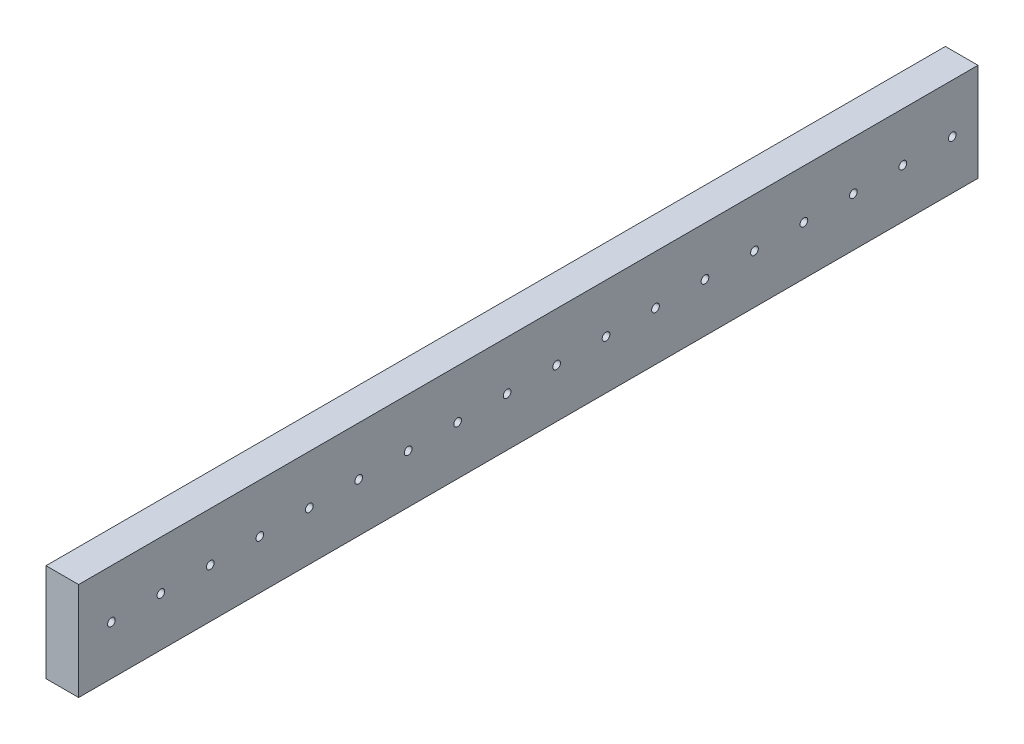
SolidWorks part; units mm, degrees
ref_plane "Alzado" through (0, 0, 0) normal (0, 0, 1) x (1, 0, 0)
ref_plane "Planta" through (0, 0, 0) normal (0, 1, 0) x (1, 0, 0)
ref_plane "Vista lateral" through (0, 0, 0) normal (1, 0, 0) x (0, 0, -1)
sketch "Croquis2" plane through (0, 0, 0) normal (0, 0, 1) x (1, 0, 0)
  line L1 (-12.7, -38.1) -> (12.7, -38.1)
  line L2 (-12.7, -38.1) -> (-12.7, 38.1)
  line L3 (-12.7, 38.1) -> (12.7, 38.1)
  line L4 (12.7, -38.1) -> (12.7, 38.1)
  line L5 (-12.7, -38.1) -> (12.7, 38.1) construction
  line L6 (-12.7, 38.1) -> (12.7, -38.1) construction
  point P0 (0, 0)
  dimension "D1" = 25.4
  dimension "D2" = 76.2
extrude "Saliente-Extruir1" add sketch "Croquis2" against normal blind 700
sketch "Croquis3" plane through (-12.7, 0, 0) normal (-1, 0, 0) x (0, 0, 1)
  line L0 (-700, 0) -> (-680, 0) construction
  line L1 (-700, 38.1) -> (-700, -38.1) construction
  circle A0 centre (-680, 0) radius 3
  circle A1 centre (-641.5, 0) radius 3
  circle A2 centre (-603, 0) radius 3
  circle A3 centre (-564.5, 0) radius 3
  circle A4 centre (-526, 0) radius 3
  circle A5 centre (-487.5, 0) radius 3
  circle A6 centre (-449, 0) radius 3
  circle A7 centre (-410.5, 0) radius 3
  circle A8 centre (-372, 0) radius 3
  circle A9 centre (-333.5, 0) radius 3
  circle A10 centre (-295, 0) radius 3
  circle A11 centre (-256.5, 0) radius 3
  circle A12 centre (-218, 0) radius 3
  circle A13 centre (-179.5, 0) radius 3
  circle A14 centre (-141, 0) radius 3
  circle A15 centre (-102.5, 0) radius 3
  circle A16 centre (-64, 0) radius 3
  circle A17 centre (-25.5, 0) radius 3
  dimension "D1" = 6
  dimension "D2" = 20
  dimension "D4" = 38.5
  dimension "D3" = 18
extrude "Cortar-Extruir1" cut sketch "Croquis3" against normal through all
